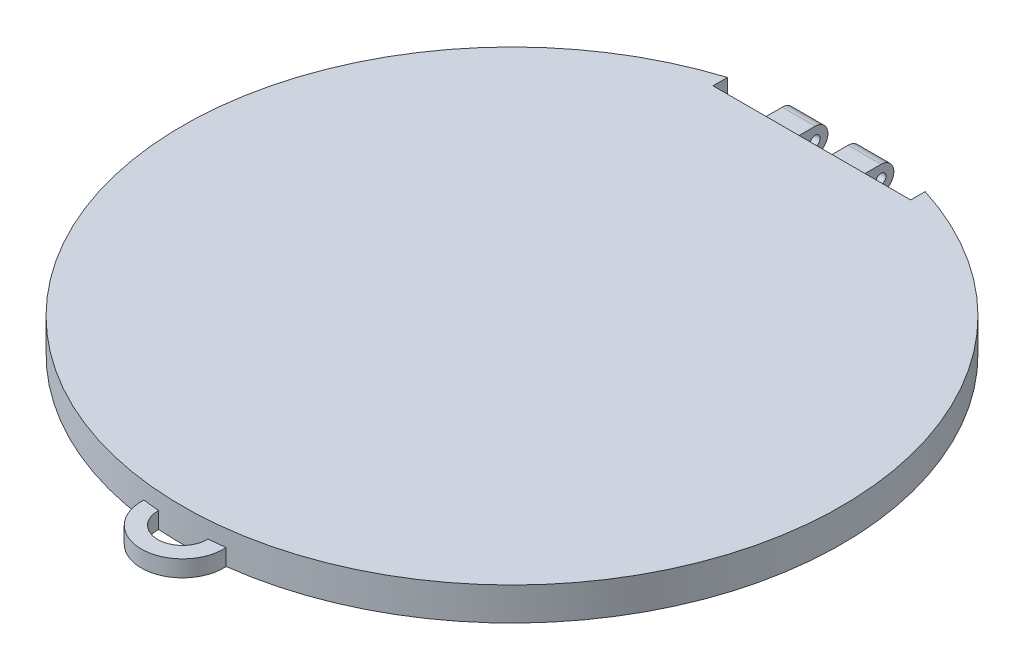
SolidWorks part; units mm, degrees
material "ABS"
ref_plane "Front Plane" through (0, 0, 0) normal (0, 0, 1) x (1, 0, 0)
ref_plane "Top Plane" through (0, 0, 0) normal (0, 1, 0) x (1, 0, 0)
ref_plane "Right Plane" through (0, 0, 0) normal (1, 0, 0) x (0, 0, -1)
sketch "Sketch1" plane through (0, 0, 0) normal (0, 1, 0) x (1, 0, 0)
  circle A0 centre (0, 0) radius 100
  dimension "D1" = 200
extrude "Boss-Extrude1" add sketch "Sketch1" against normal blind 10
sketch "Sketch3" plane through (0, 0, 0) normal (0, 1, 0) x (1, 0, 0)
  line L0 (0, 0) -> (0, 100) construction
  line L2 (30, 91) -> (-30, 91)
  line L3 (30, 91) -> (30, 109)
  line L4 (30, 109) -> (-30, 109)
  line L5 (-30, 91) -> (-30, 109)
  line L6 (30, 91) -> (-30, 109) construction
  line L7 (30, 109) -> (-30, 91) construction
  point P7 (0, 100)
  dimension "D1" = 100
  dimension "D2" = 60
  dimension "D3" = 18
extrude "Cut-Extrude1" cut sketch "Sketch3" against normal through all
sketch "Sketch4" plane through (0, 0, -91) normal (0, 0, -1) x (-1, 0, 0)
  line L0 (0, -10) -> (5, -10) construction
  line L1 (30, -10) -> (-30, -10) construction
  line L2 (5, -10) -> (5, -4.12)
  line L3 (5, -4.12) -> (15, -4.12)
  line L4 (15, -4.12) -> (15, -10)
  line L5 (15, -10) -> (5, -10)
  line L6 (0, -10) -> (-5, -10) construction
  line L7 (-5, -10) -> (-5, -4.12)
  line L8 (-5, -4.12) -> (-15, -4.12)
  line L9 (-15, -4.12) -> (-15, -10)
  line L10 (-15, -10) -> (-5, -10)
  dimension "D1" = 5
  dimension "D2" = 5.88
  dimension "D3" = 10
  dimension "D4" = 5
  dimension "D5" = 10
extrude "Boss-Extrude2" add sketch "Sketch4" along normal blind 2.12
sketch "Sketch5" plane through (-5, 0, 0) normal (1, 0, 0) x (0, 0, -1)
  line L0 (93.12, -10) -> (93.12, -8) construction
  line L1 (93.12, -4.12) -> (93.12, -10) construction
  line L2 (93.12, -8) -> (97, -8) construction
  circle A0 centre (97, -8) radius 3.88
  dimension "D3" = 7.76
  dimension "D1" = 2
  dimension "D2" = 3.88
extrude "Boss-Extrude3" add sketch "Sketch5" against normal blind 10 separate body
sketch "Sketch6" plane through (15, 0, 0) normal (1, 0, 0) x (0, 0, -1)
  line L0 (93.12, -10) -> (93.12, -8) construction
  line L1 (93.12, -4.12) -> (93.12, -10) construction
  line L2 (93.12, -8) -> (97, -8) construction
  circle A0 centre (97, -8) radius 3.88
  dimension "D3" = 7.76
  dimension "D1" = 2
  dimension "D2" = 3.88
extrude "Boss-Extrude4" add sketch "Sketch6" against normal blind 10 separate body
sketch "Sketch7" plane through (15, 0, 0) normal (1, 0, 0) x (0, 0, -1)
  circle A0 centre (97, -8) radius 1.5
  dimension "D1" = 3
extrude "Cut-Extrude2" cut sketch "Sketch7" against normal through all
sketch "Sketch8" plane through (0, 0, -93.12) normal (0, 0, -1) x (-1, 0, 0)
  line L1 (5, -4.12) -> (15, -4.12)
  line L2 (5, -4.12) -> (5, -10)
  line L3 (5, -10) -> (15, -10)
  line L4 (15, -4.12) -> (15, -10)
extrude "Boss-Extrude5" add sketch "Sketch8" along normal up to surface (3.88 mm away)
sketch "Sketch9" plane through (0, 0, -93.12) normal (0, 0, -1) x (-1, 0, 0)
  line L1 (-15, -4.12) -> (-5, -4.12)
  line L2 (-15, -4.12) -> (-15, -10)
  line L3 (-15, -10) -> (-5, -10)
  line L4 (-5, -4.12) -> (-5, -10)
extrude "Boss-Extrude6" add sketch "Sketch9" along normal up to surface (3.88 mm away) up to face at (5, -4.12, -97)
sketch "Sketch12" plane through (0, -10, 0) normal (0, -1, 0) x (-1, 0, 0)
  line L0 (30, 95.3939) -> (30, 91)
  line L1 (30, 91) -> (-30, 91)
  line L2 (-30, 91) -> (-30, 95.3939)
  arc A0 (-30, 95.3939) -> (30, 95.3939) centre (0, 0) ccw
extrude "Boss-Extrude8" add sketch "Sketch12" along normal blind 3
sketch "Sketch13" plane through (0, 0, 0) normal (0, 1, 0) x (1, 0, 0)
  line L0 (-30, 95.3939) -> (-30, 91)
  line L1 (-30, 91) -> (30, 91)
  line L2 (30, 91) -> (30, 95.3939)
  arc A0 (-30, 95.3939) -> (30, 95.3939) centre (0, 0) ccw
extrude "Cut-Extrude3" cut sketch "Sketch13" against normal blind 3
sketch "Sketch15" [suppressed] plane through (0, -3, 0) normal (0, 1, 0) x (1, 0, 0)
  line L0 (0, 0) -> (0, -100) construction
  line L1 (0, -100) -> (16.58, -100)
  line L6 (16.58, -100) -> (16.58, -105)
  line L7 (16.58, -105) -> (-13.42, -105)
  line L8 (-13.42, -105) -> (-13.42, -100)
  line L9 (-13.42, -100) -> (16.58, -100)
  arc A0 (-30, 95.3939) -> (30, 95.3939) centre (0, 0) ccw construction
  dimension "D1" = 16.58
  dimension "D2" = 5
  dimension "D3" = 30
  dimension "D4" = 5
extrude "Boss-Extrude9" [suppressed] add sketch "Sketch15" against normal blind 10 separate body contours L9 L8 L7 L6 L1
ref_plane "Plane2" through (0, 0, 100) normal (0, 0, 1) x (1, 0, 0)
sketch "Sketch17" [suppressed] plane through (0, 0, 100) normal (0, 0, 1) x (1, 0, 0)
  line L0 (0, -3.1684) -> (0, -8.1684) construction
  line L1 (0, -8.1684) -> (10, -8.1684) construction
  line L2 (0, -8.1684) -> (-10, -8.1684) construction
  circle A0 centre (10, -8.1684) radius 2.5
  circle A1 centre (-10, -8.1684) radius 2.5
  point P7 (0, 0)
  dimension "D4" = 5
  dimension "D5" = 5
  dimension "D1" = 5
  dimension "D2" = 10
  dimension "D3" = 10
sketch "Sketch18" [suppressed] plane through (0, 0, 0) normal (1, 0, 0) x (0, 0, -1)
  line L0 (-100, -8.1684) -> (-110, -8.1684) construction
  line L1 (-100, -5.6684) -> (-100, -10.6684) construction
  circle A0 centre (-110, -8.1684) radius 2.5
  dimension "D2" = 5
  dimension "D1" = 10
sketch3d "3DSketch1" [suppressed]
  arc A0 (-10, -8.1684, 100) -> (10, -8.1684, 100) centre (0, -8.1684, 100) cw
  point P2 (0, 1.8316, 100)
sweep "Sweep2" [suppressed] add profiles "Sketch18" path "3DSketch1"
sketch "Sketch22" plane through (0, -13, 0) normal (0, -1, 0) x (-1, 0, 0)
  line L0 (-5.5, -100) -> (5.5, -100) construction
  circle A0 centre (0, -100) radius 12.5
  circle A1 centre (0, -100) radius 7.5
  dimension "D1" = 25
  dimension "D2" = 15
extrude "Boss-Extrude10" add sketch "Sketch22" against normal blind 5
